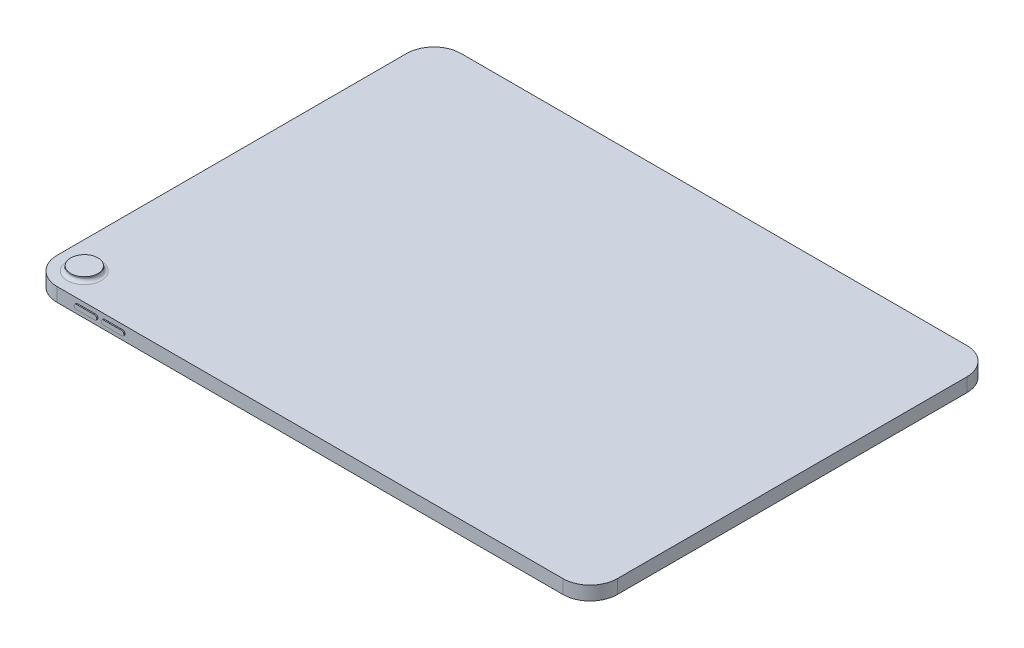
SolidWorks part; units mm, degrees
ref_plane "Ebene vorne" through (0, 0, 0) normal (0, 0, 1) x (1, 0, 0)
ref_plane "Ebene oben" through (0, 0, 0) normal (0, 1, 0) x (1, 0, 0)
ref_plane "Ebene rechts" through (0, 0, 0) normal (1, 0, 0) x (0, 0, -1)
sketch "Skizze1" plane through (0, 0, 0) normal (0, 1, 0) x (1, 0, 0)
  line L0 (-123.8, 0) -> (123.8, 0) construction
  line L1 (-123.8, 89.25) -> (123.8, 89.25)
  line L2 (-123.8, 89.25) -> (-123.8, -89.25)
  line L3 (-123.8, -89.25) -> (123.8, -89.25)
  line L4 (123.8, 89.25) -> (123.8, -89.25)
  line L5 (0, 89.25) -> (0, -89.25) construction
  dimension "D1" = 0
  dimension "D2" = 178.5
  dimension "D3" = 0
  dimension "D4" = 247.6
extrude "Aufsatz-Linear austragen1" add sketch "Skizze1" along normal blind 6.1
fillet "Verrundung1" radius 12 4 edges at (-123.8, 3.05, -89.25) (-123.8, 3.05, 89.25) (123.8, 3.05, -89.25) (123.8, 3.05, 89.25)
sketch "Skizze2" plane through (0, 6.1, 0) normal (0, 1, 0) x (1, 0, 0)
  line L0 (-111.8, -89.25) -> (111.8, -89.25) construction
  line L1 (-123.8, 77.25) -> (-123.8, -77.25) construction
  circle A0 centre (-111.8, -77.25) radius 6
  dimension "D3" = 12
  dimension "D1" = 12
  dimension "D2" = 12
extrude "Aufsatz-Linear austragen2" add sketch "Skizze2" along normal blind 2
fillet "Verrundung2" radius 1.5 1 edges at (-111.8, 6.1, 83.25)
sketch "Skizze3" plane through (-123.8, 0, 0) normal (-1, 0, 0) x (0, 0, 1)
  line L0 (74.4, 1.2) -> (61.1, 1.2)
  line L1 (74.4, 4.9) -> (61.1, 4.9)
  line L2 (-77.25, 0) -> (77.25, 0) construction
  line L3 (-77.25, 6.1) -> (77.25, 6.1) construction
  line L4 (89.25, 6.1) -> (89.25, 0) construction
  line L5 (77.25, 3.05) -> (74.4, 3.05) construction
  line L6 (77.25, 0) -> (77.25, 6.1) construction
  arc A0 (74.4, 1.2) -> (74.4, 4.9) centre (74.4, 3.05) ccw
  arc A1 (61.1, 4.9) -> (61.1, 1.2) centre (61.1, 3.05) ccw
  point P12 (59.25, 3.05)
  dimension "D3" = 13.3
  dimension "D1" = 3.7
  dimension "D2" = 30
extrude "Aufsatz-Linear austragen3" add sketch "Skizze3" along normal blind 0.5 contours L0 A1 L1 A0
sketch "Skizze4" plane through (0, 0, 89.25) normal (0, 0, 1) x (1, 0, 0)
  line L0 (-102.8, 4.05) -> (-94.8, 4.05)
  line L1 (-102.8, 2.05) -> (-94.8, 2.05)
  line L2 (-90.8, 4.05) -> (-82.8, 4.05)
  line L3 (-90.8, 2.05) -> (-82.8, 2.05)
  line L4 (-111.8, 6.1) -> (111.8, 6.1) construction
  line L5 (-111.8, 0) -> (111.8, 0) construction
  line L6 (-111.8, 3.05) -> (-102.8, 3.05) construction
  line L7 (-111.8, 6.1) -> (-111.8, 0) construction
  line L8 (-94.8, 3.05) -> (-90.8, 3.05) construction
  line L9 (-123.8, 0) -> (-123.8, 6.1) construction
  arc A0 (-102.8, 4.05) -> (-102.8, 2.05) centre (-102.8, 3.05) ccw
  arc A1 (-94.8, 2.05) -> (-94.8, 4.05) centre (-94.8, 3.05) ccw
  arc A2 (-90.8, 4.05) -> (-90.8, 2.05) centre (-90.8, 3.05) ccw
  arc A3 (-82.8, 2.05) -> (-82.8, 4.05) centre (-82.8, 3.05) ccw
  point P17 (-91.8, 3.05)
  point P20 (-81.8, 3.05)
  point P21 (-103.8, 3.05)
  point P22 (-93.8, 3.05)
  dimension "D1" = 2
  dimension "D2" = 2
  dimension "D3" = 10
  dimension "D4" = 10
  dimension "D5" = 42
  dimension "D6" = 2
extrude "Aufsatz-Linear austragen5" add sketch "Skizze4" along normal blind 0.5
